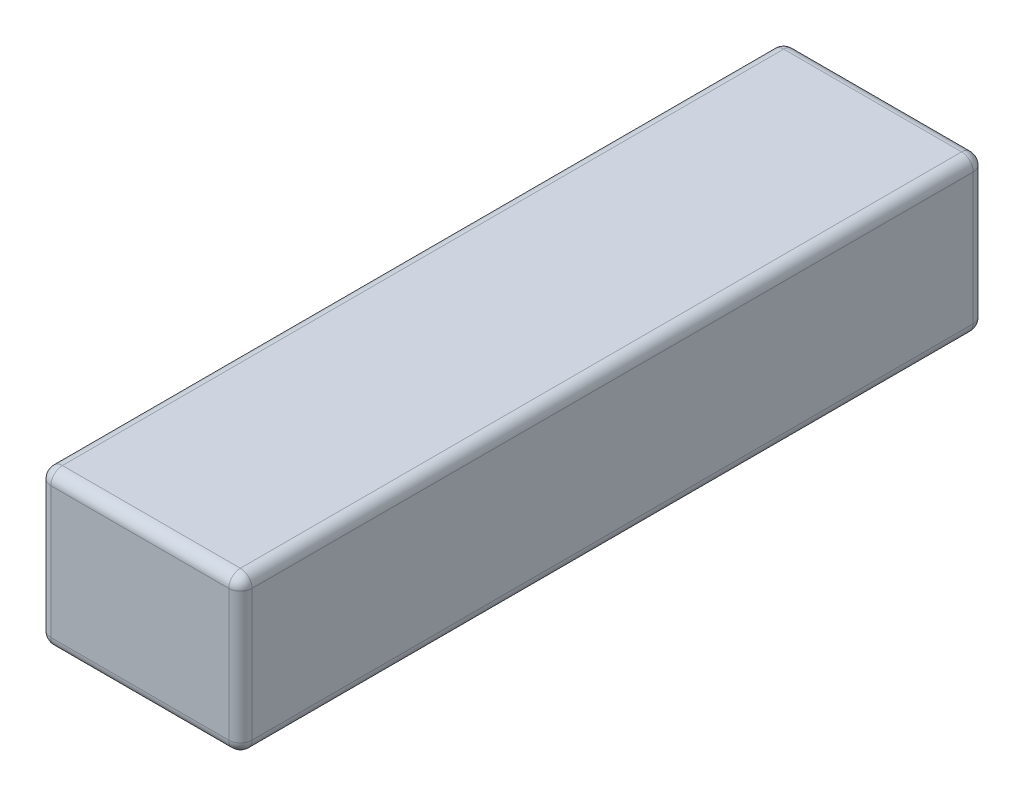
SolidWorks part; units mm, degrees
ref_plane "Ebene vorne" through (0, 0, 0) normal (0, 0, 1) x (1, 0, 0)
ref_plane "Ebene oben" through (0, 0, 0) normal (0, 1, 0) x (1, 0, 0)
ref_plane "Ebene rechts" through (0, 0, 0) normal (1, 0, 0) x (0, 0, -1)
sketch "Skizze1" plane through (0, 0, 0) normal (0, 0, 1) x (1, 0, 0)
  line L1 (-8.65, 6.65) -> (8.65, 6.65)
  line L2 (-8.65, 6.65) -> (-8.65, -6.65)
  line L3 (-8.65, -6.65) -> (8.65, -6.65)
  line L4 (8.65, 6.65) -> (8.65, -6.65)
  dimension "D1" = 6.65
  dimension "D2" = 13.3
  dimension "D3" = 8.65
  dimension "D4" = 17.3
extrude "Aufsatz-Linear austragen1" add sketch "Skizze1" along normal blind 64
fillet "Verrundung1" radius 1 12 edges at (-8.65, -6.65, 32) (8.65, -6.65, 32) (8.65, 6.65, 32) (-8.65, 6.65, 32) (0, 6.65, 64) (8.65, 0, 64) (0, -6.65, 64) (-8.65, 0, 64) (0, 6.65, 0) (8.65, 0, 0) (0, -6.65, 0) (-8.65, 0, 0)
